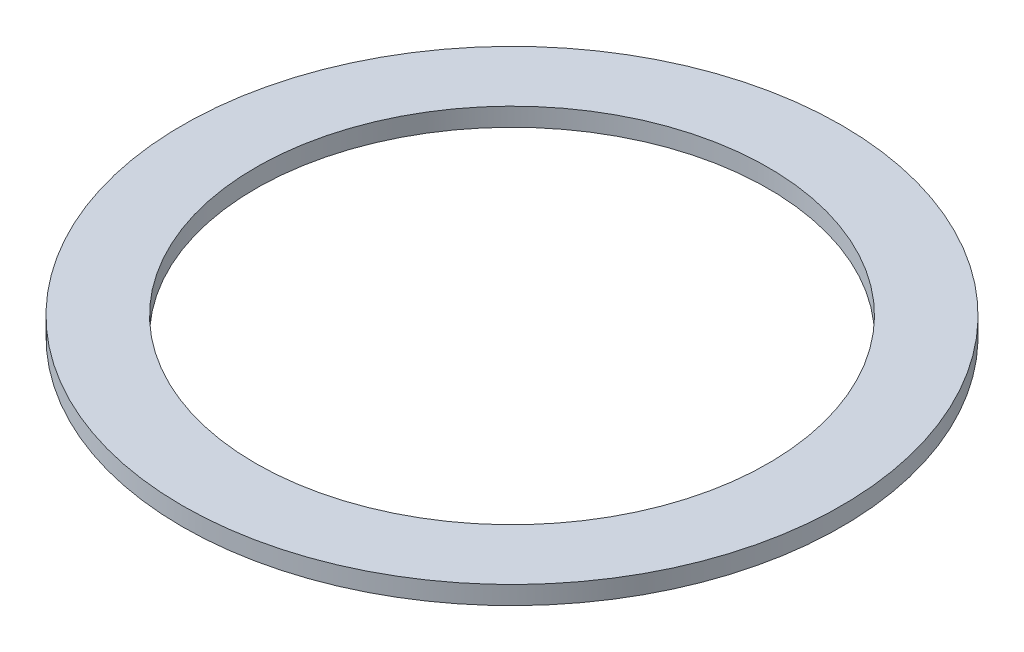
SolidWorks part; units mm, degrees
ref_plane "Front Plane" through (0, 0, 0) normal (0, 0, 1) x (1, 0, 0)
ref_plane "Top Plane" through (0, 0, 0) normal (0, 1, 0) x (1, 0, 0)
ref_plane "Right Plane" through (0, 0, 0) normal (1, 0, 0) x (0, 0, -1)
sketch "Sketch1" plane through (0, 0, 0) normal (0, 1, 0) x (1, 0, 0)
  circle A0 centre (0, 0) radius 90
  circle A1 centre (0, 0) radius 70
  dimension "D1" = 180
  dimension "D2" = 140
extrude "Boss-Extrude1" add sketch "Sketch1" along normal blind 5
sketch "Sketch2" plane through (0, 5, 0) normal (0, 1, 0) x (1, 0, 0)
  line L0 (0, 0) -> (0, 90) construction
  line L2 (-3.7219, 87.5) -> (3.7219, 87.5)
  line L3 (-3.7219, 87.5) -> (-3.7219, 72.5)
  line L4 (-3.7219, 72.5) -> (3.7219, 72.5)
  line L5 (3.7219, 87.5) -> (3.7219, 72.5)
  line L6 (-3.7219, 87.5) -> (3.7219, 72.5) construction
  line L7 (-3.7219, 72.5) -> (3.7219, 87.5) construction
  circle A0 centre (0, 0) radius 90 construction
  point P6 (0, 80)
  point P11 (0, 80.3708)
  dimension "D1" = 2.5
  dimension "D2" = 15
